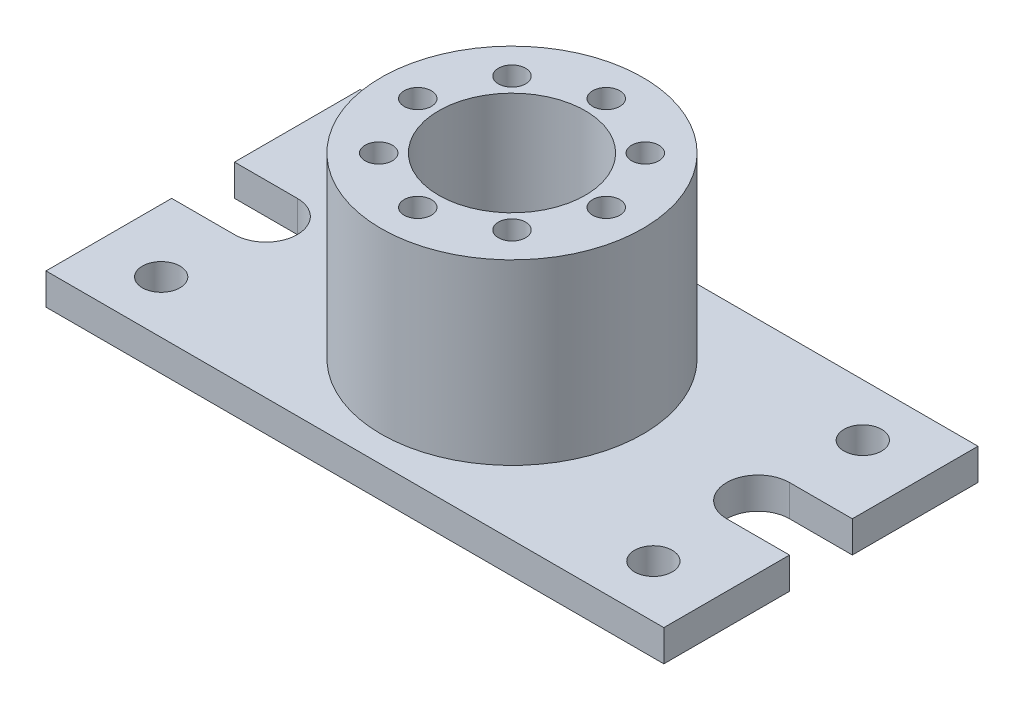
SolidWorks part; units mm, degrees
ref_plane "Front Plane" through (0, 0, 0) normal (0, 0, 1) x (1, 0, 0)
ref_plane "Top Plane" through (0, 0, 0) normal (0, 1, 0) x (1, 0, 0)
ref_plane "Right Plane" through (0, 0, 0) normal (1, 0, 0) x (0, 0, -1)
sketch "Sketch1" plane through (0, 0, 0) normal (0, 1, 0) x (1, 0, 0)
  line L0 (0, 146.427) -> (0, -120.4847) construction
  line L1 (-147.5, -75) -> (147.5, -75)
  line L2 (-147.5, -75) -> (-147.5, -15)
  line L3 (-147.5, 75) -> (147.5, 75)
  line L4 (147.5, -75) -> (147.5, 75)
  line L5 (-147.5, -75) -> (147.5, 75) construction
  line L6 (-147.5, 75) -> (147.5, -75) construction
  line L7 (-220.5723, 0) -> (195.3514, 0) construction
  line L8 (-117.5, 15) -> (-147.5, 15)
  line L9 (-117.5, -15) -> (-147.5, -15)
  line L10 (-147.5, 15) -> (-147.5, 75)
  line L11 (117.5, 15) -> (147.5, 15)
  line L12 (117.5, -15) -> (147.5, -15)
  circle A0 centre (-117.5, 50) radius 9
  circle A1 centre (117.5, 50) radius 9
  circle A2 centre (117.5, -50) radius 9
  circle A3 centre (-117.5, -50) radius 9
  arc A4 (-117.5, -15) -> (-117.5, 15) centre (-117.5, 0) ccw
  arc A5 (117.5, -15) -> (117.5, 15) centre (117.5, 0) cw
  point P0 (0, 0)
  dimension "D3" = 18
  dimension "D4" = 30
  dimension "D1" = 295
  dimension "D2" = 150
  dimension "D5" = 30
  dimension "D6" = 30
  dimension "D7" = 100
extrude "Boss-Extrude1" add sketch "Sketch1" along normal blind 15 contours L12 A5 L11 L4 L3 L10 L8 A4 L9 L2 L1 A1 A0 A2 A3
sketch "Sketch2" plane through (0, 15, 0) normal (0, 1, 0) x (1, 0, 0)
  circle A0 centre (0, 0) radius 62.5
  dimension "D1" = 125
extrude "Boss-Extrude2" add sketch "Sketch2" along normal blind 85
sketch "Sketch3" plane through (0, 100, 0) normal (0, 1, 0) x (1, 0, 0)
  circle A0 centre (0, 0) radius 35
  dimension "D1" = 70
extrude "Cut-Extrude1" cut sketch "Sketch3" against normal through all
sketch "Sketch4" plane through (0, 100, 0) normal (0, 1, 0) x (1, 0, 0)
  line L0 (0, 0) -> (-45, 0) construction
  circle A0 centre (0, 0) radius 45 construction
  circle A1 centre (-45, 0) radius 6.5
  circle A2 centre (-31.8198, 31.8198) radius 6.5
  circle A3 centre (0, 45) radius 6.5
  circle A4 centre (31.8198, 31.8198) radius 6.5
  circle A5 centre (45, 0) radius 6.5
  circle A6 centre (31.8198, -31.8198) radius 6.5
  circle A7 centre (0, -45) radius 6.5
  circle A8 centre (-31.8198, -31.8198) radius 6.5
  dimension "D1" = 90
  dimension "D2" = 13
  dimension "D4" = 45
  dimension "D3" = 8
extrude "Cut-Extrude2" cut sketch "Sketch4" against normal blind 50
